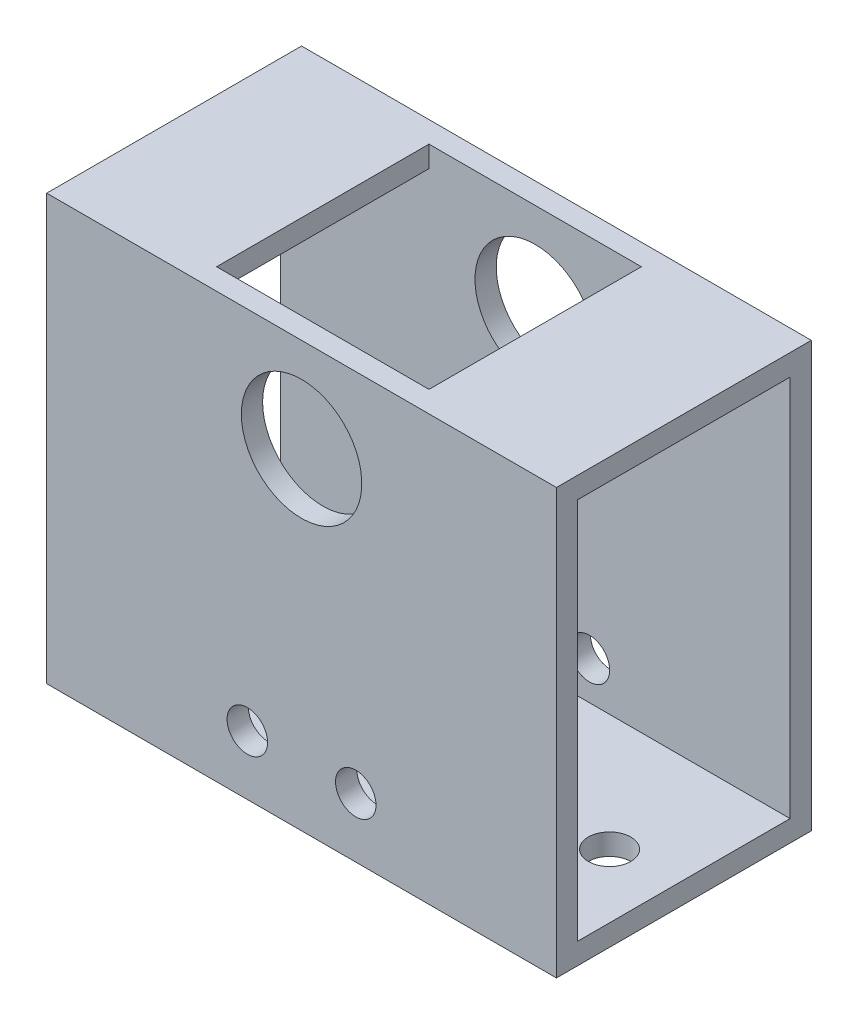
SolidWorks part; units mm, degrees
ref_plane "Front Plane" through (0, 0, 0) normal (0, 0, 1) x (1, 0, 0)
ref_plane "Top Plane" through (0, 0, 0) normal (0, 1, 0) x (1, 0, 0)
ref_plane "Right Plane" through (0, 0, 0) normal (1, 0, 0) x (0, 0, -1)
sketch "Sketch1" plane through (0, 0, 0) normal (1, 0, 0) x (0, 0, -1)
  line L0 (-15.875, -28.575) -> (-15.875, 28.575)
  line L1 (-19.05, -31.75) -> (19.05, -31.75)
  line L2 (-19.05, -31.75) -> (-19.05, 31.75)
  line L3 (-19.05, 31.75) -> (19.05, 31.75)
  line L4 (19.05, -31.75) -> (19.05, 31.75)
  line L5 (-19.05, -31.75) -> (19.05, 31.75) construction
  line L6 (-19.05, 31.75) -> (19.05, -31.75) construction
  line L7 (-15.875, 28.575) -> (15.875, 28.575)
  line L8 (15.875, -28.575) -> (15.875, 28.575)
  line L9 (-15.875, -28.575) -> (15.875, -28.575)
  point P0 (0, 0)
  dimension "D1" = 38.1
  dimension "D2" = 63.5
  dimension "D3" = 3.175
extrude "Boss-Extrude1" add sketch "Sketch1" along normal blind 76.2
sketch "Sketch2" plane through (0, 0, 0) normal (0, 0, 1) x (1, 0, 0)
  line L0 (38.1, 31.75) -> (38.1, 17.7) construction
  line L1 (76.2, 31.75) -> (0, 31.75) construction
  line L2 (38.1, -31.75) -> (38.1, -22.86) construction
  line L3 (76.2, -31.75) -> (0, -31.75) construction
  line L4 (29.995, -22.86) -> (46.205, -22.86) construction
  line L5 (33.02, -22.86) -> (43.18, -22.86) construction
  circle A0 centre (38.1, 17.7) radius 9
  circle A1 centre (46.205, -22.86) radius 3.025
  circle A2 centre (29.995, -22.86) radius 3.025
  circle A3 centre (29.995, -22.86) radius 4.7625 construction
  point P12 (38.1, -22.86)
  dimension "D2" = 18
  dimension "D3" = 6.05
  dimension "D5" = 9.525
  dimension "D1" = 14.05
  dimension "D4" = 10.16
  dimension "D6" = 8.89
extrude "Cut-Extrude1" cut sketch "Sketch2" against normal mid plane 76.2
sketch "Sketch3" plane through (0, 0, 0) normal (0, 1, 0) x (1, 0, 0)
  line L0 (38.1, 19.05) -> (38.1, -19.05) construction
  line L1 (76.2, 19.05) -> (0, 19.05) construction
  line L2 (76.2, -19.05) -> (0, -19.05) construction
  line L3 (76.2, 15.875) -> (0, 15.875) construction
  line L4 (76.2, 19.05) -> (76.2, -19.05) construction
  line L5 (76.2, 0) -> (0, 0) construction
  line L6 (22.225, -15.875) -> (53.975, -15.875)
  line L7 (22.225, -15.875) -> (22.225, 15.875)
  line L8 (22.225, 15.875) -> (53.975, 15.875)
  line L9 (53.975, -15.875) -> (53.975, 15.875)
  line L10 (22.225, -15.875) -> (53.975, 15.875) construction
  line L11 (22.225, 15.875) -> (53.975, -15.875) construction
  point P11 (38.1, 0)
  dimension "D1" = 31.75
extrude "Cut-Extrude2" cut sketch "Sketch3" along normal blind 76.2
sketch "Sketch4" plane through (0, 0, 0) normal (0, 1, 0) x (1, 0, 0)
  line L0 (38.1, 15.875) -> (38.1, -19.05) construction
  line L1 (76.2, 15.875) -> (0, 15.875) construction
  line L2 (76.2, -19.05) -> (0, -19.05) construction
  line L3 (9.525, -1.5875) -> (66.675, -1.5875) construction
  circle A0 centre (9.525, -1.5875) radius 3.175
  circle A1 centre (66.675, -1.5875) radius 3.175
  point P9 (38.1, -1.5875)
  dimension "D1" = 6.35
  dimension "D2" = 28.575
extrude "Cut-Extrude3" cut sketch "Sketch4" against normal through all
